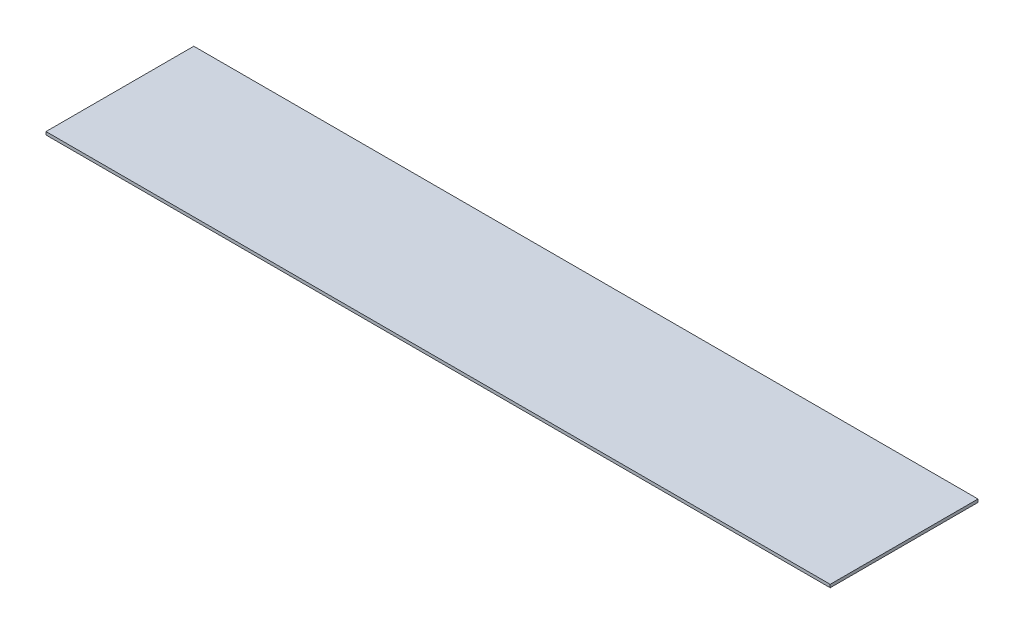
SolidWorks part; units mm, degrees
ref_plane "Front Plane" through (0, 0, 0) normal (0, 0, 1) x (1, 0, 0)
ref_plane "Top Plane" through (0, 0, 0) normal (0, 1, 0) x (1, 0, 0)
ref_plane "Right Plane" through (0, 0, 0) normal (1, 0, 0) x (0, 0, -1)
sketch "Sketch1" plane through (0, 0, 0) normal (0, 1, 0) x (1, 0, 0)
  line L1 (-106.3158, 50.7895) -> (153.6842, 50.7895)
  line L2 (-106.3158, 50.7895) -> (-106.3158, 1.7895)
  line L3 (-106.3158, 1.7895) -> (153.6842, 1.7895)
  line L4 (153.6842, 50.7895) -> (153.6842, 1.7895)
  dimension "D1" = 260
  dimension "D2" = 49
extrude "Boss-Extrude1" add sketch "Sketch1" along normal blind 1
